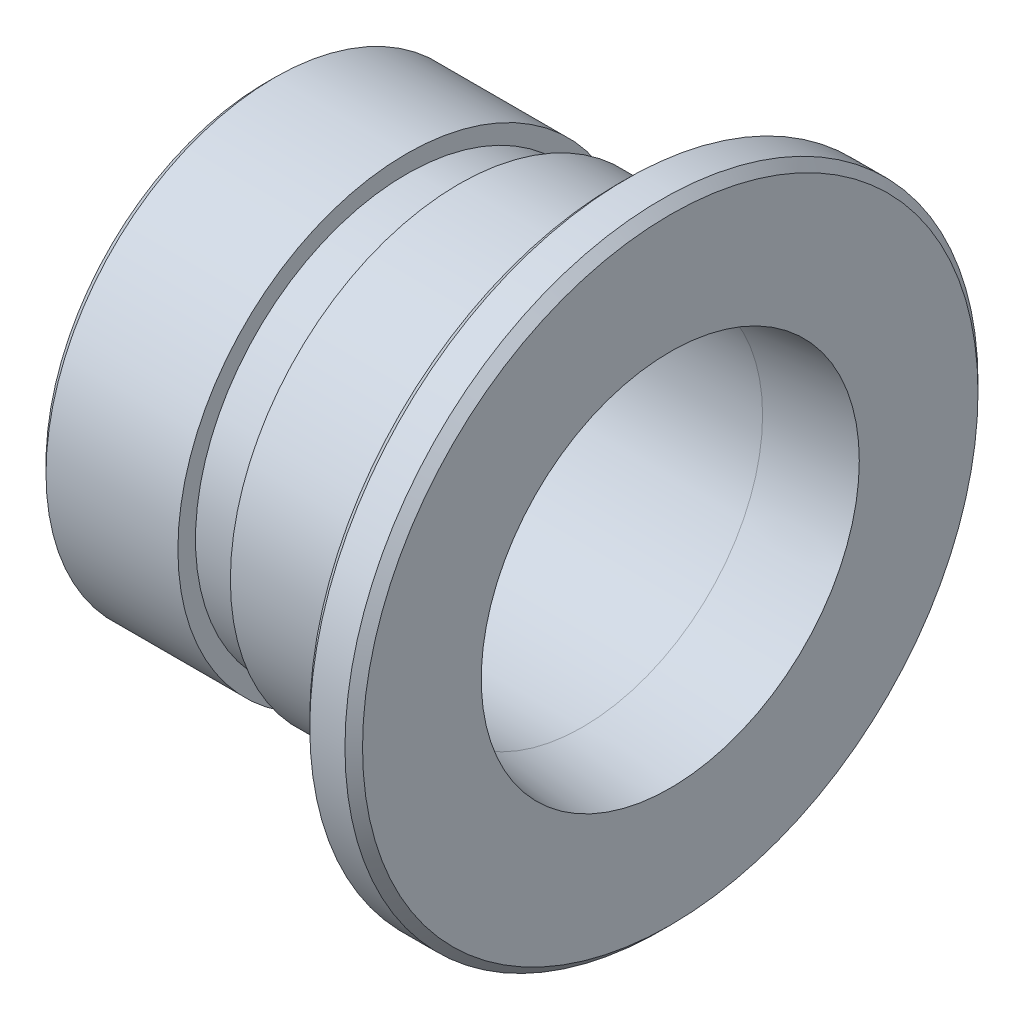
SolidWorks part; units mm, degrees
material "PVC rigide"
ref_plane "Plan de face" through (0, 0, 0) normal (0, 0, 1) x (1, 0, 0)
ref_plane "Plan de dessus" through (0, 0, 0) normal (0, 1, 0) x (1, 0, 0)
ref_plane "Plan de droite" through (0, 0, 0) normal (1, 0, 0) x (0, 0, -1)
sketch "Esquisse1" plane through (0, 0, 0) normal (0, 0, 1) x (1, 0, 0)
  line L0 (0, 0) -> (-27.0844, 0) construction
  line L1 (0, 10.75) -> (0, 17.5)
  line L2 (-0.5, 18) -> (-2.5, 18)
  line L3 (-3, 17.5) -> (-3, 13)
  line L4 (-3, 13) -> (-12.0158, 13)
  line L5 (-12.0158, 13) -> (-11.9842, 12)
  line L6 (-11.9842, 12) -> (-15, 12)
  line L7 (-15, 12) -> (-15, 13)
  line L8 (-15, 13) -> (-22.5, 13)
  line L9 (-23, 12.5) -> (-23, 10.75)
  line L10 (-18, 10.25) -> (-5, 10.25)
  line L11 (0, 17.5) -> (-0.5, 18)
  line L12 (-22.5, 13) -> (-23, 12.5)
  line L13 (-5, 10.25) -> (0, 10.75)
  line L14 (-23, 10.75) -> (-18, 10.25)
  line L15 (-2.5, 18) -> (-3, 17.5)
  point P3 (0, 10.25)
  point P4 (0, 18)
  point P5 (-13.4921, 12)
  point P6 (-3, 18)
  point P12 (-23, 13)
  point P13 (-23, 10.25)
  point P14 (-12, 12.5)
  point P15 (-27.0844, 0)
  point P16 (0, 0)
  point P25 (0, 0)
revolve "Révolution1" add sketch "Esquisse1" angle 360 about L0
equation "\"D1@Esquisse1\"=20.5/2mm"
